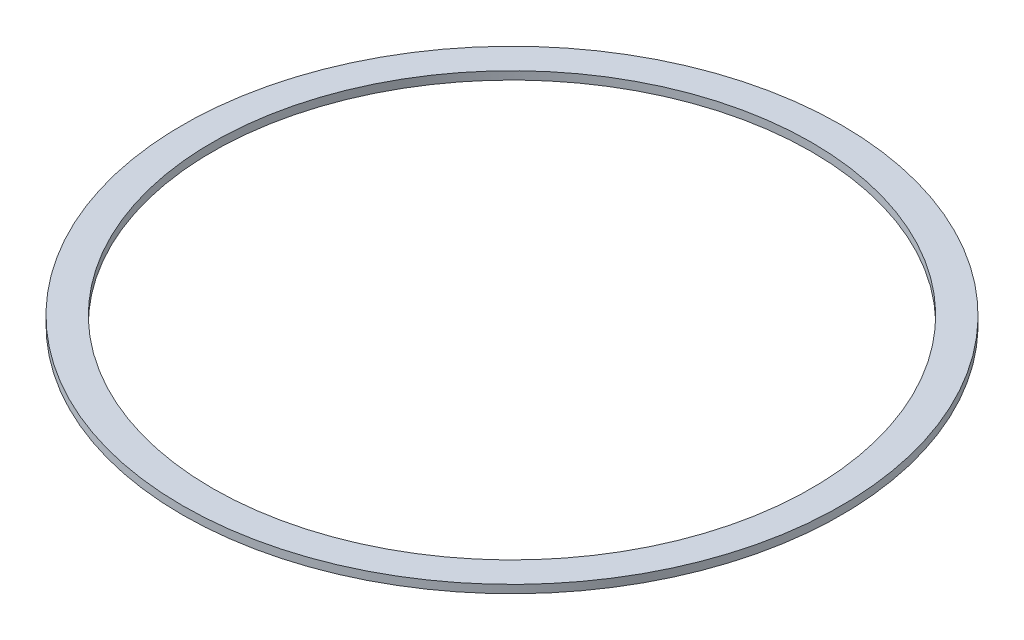
SolidWorks part; units mm, degrees
material "Oak"
ref_plane "Front Plane" through (0, 0, 0) normal (0, 0, 1) x (1, 0, 0)
ref_plane "Top Plane" through (0, 0, 0) normal (0, 1, 0) x (1, 0, 0)
ref_plane "Right Plane" through (0, 0, 0) normal (1, 0, 0) x (0, 0, -1)
sketch "Sketch1" plane through (0, 0, 0) normal (0, 1, 0) x (1, 0, 0)
  circle A0 centre (0, 0) radius 88.9
  circle A1 centre (0, 0) radius 97.79
  dimension "D1" = 177.8
  dimension "D2" = 195.58
extrude "Boss-Extrude1" add sketch "Sketch1" along normal blind 2.4
